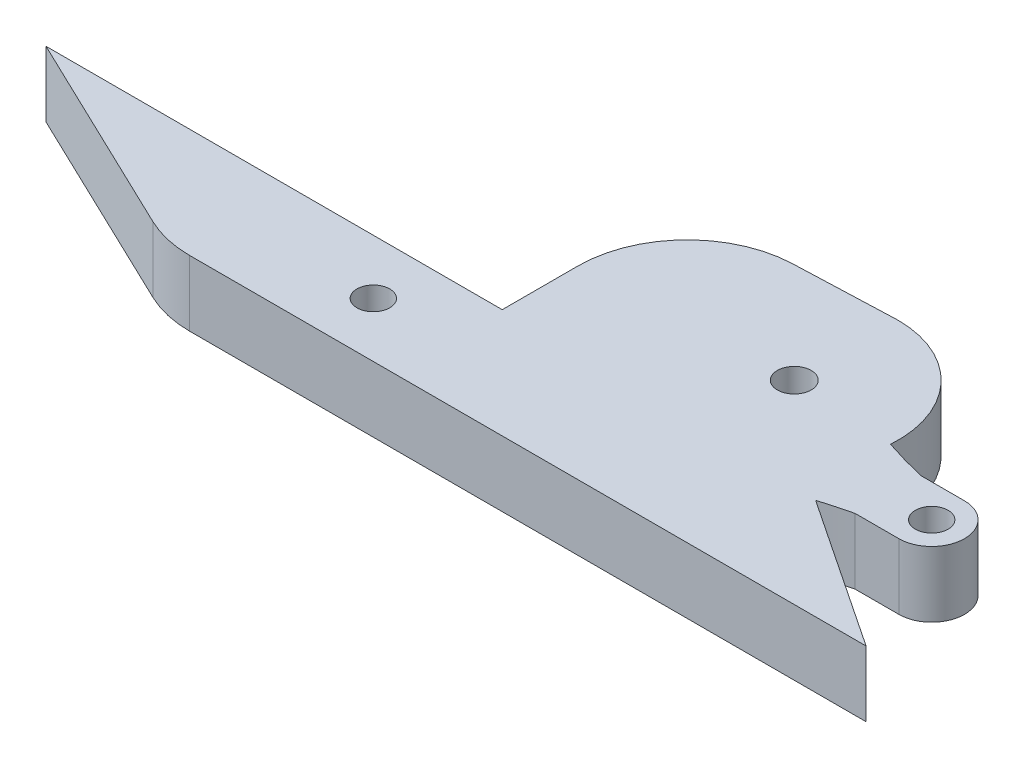
SolidWorks part; units mm, degrees
ref_plane "Front Plane" through (0, 0, 0) normal (0, 0, 1) x (1, 0, 0)
ref_plane "Top Plane" through (0, 0, 0) normal (0, 1, 0) x (1, 0, 0)
ref_plane "Right Plane" through (0, 0, 0) normal (1, 0, 0) x (0, 0, -1)
sketch "Sketch1" plane through (0, 0, 0) normal (0, 1, 0) x (1, 0, 0)
  line L0 (-36.5638, -5) -> (-28.2752, -5) construction
  line L5 (-18.6546, 16.9127) -> (-9.3343, 17.2666)
  line L6 (1.1554, -0.7703) -> (15, -10)
  line L9 (0, -10) -> (-46.8648, -10)
  line L13 (0, -10) -> (15, -10)
  line L14 (-49.1376, 0) -> (-28.2752, 0)
  line L15 (-28.2752, 0) -> (-28.2752, 6.9199)
  line L16 (-49.1376, 0) -> (-70, 0)
  line L18 (4, 6) -> (8, 6)
  line L20 (0, 0) -> (8, 0)
  line L22 (-51.1872, -9.0176) -> (-70, 0)
  arc A0 (0.142, 7.0958) -> (-10.0546, 17.2392) centre (-9.3343, 7.7666) ccw
  circle A1 centre (-9.3343, 7.7666) radius 1.55
  arc A2 (-18.6546, 16.9127) -> (-28.2752, 6.9199) centre (-18.2752, 6.9199) ccw
  circle A3 centre (-35.0638, -5) radius 1.5
  arc A4 (8, 0) -> (8, 6) centre (8, 3) ccw
  circle A5 centre (8, 3) radius 1.5
  arc A6 (-46.8648, -10) -> (-51.1872, -9.0176) centre (-46.8648, 0) cw
  spline S0 degree 2 poles (0.142, 7.0958) (2.0456, 6.4586) (4, 6) knots 0 0 0 1 1 1
  spline S1 degree 3 poles (1.1554, -0.7703) (2.0945, -0.4814) (3.0427, -0.2246) (4, 0) knots 0.265251 0.265251 0.265251 0.265251 1 1 1 1
  dimension "D3" = 19
  dimension "D6" = 3.1
  dimension "D2" = 10
  dimension "D7" = 3
  dimension "D10" = 6
  dimension "D11" = 3
  dimension "D8" = 10
  dimension "D1" = 8
  dimension "D4" = 10
  dimension "D5" = 15
  dimension "D9" = 6
extrude "Boss-Extrude1" add sketch "Sketch1" along normal blind 6
